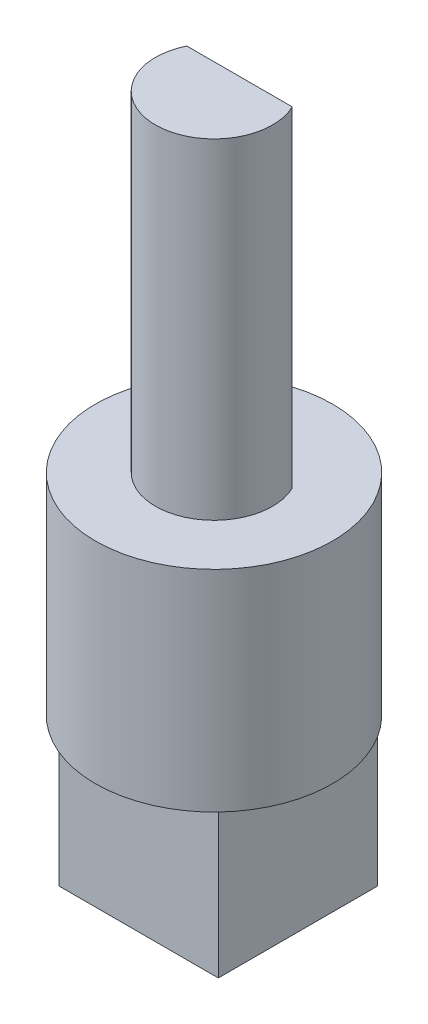
SolidWorks part; units mm, degrees
ref_plane "Front Plane" through (0, 0, 0) normal (0, 0, 1) x (1, 0, 0)
ref_plane "Top Plane" through (0, 0, 0) normal (0, 1, 0) x (1, 0, 0)
ref_plane "Right Plane" through (0, 0, 0) normal (1, 0, 0) x (0, 0, -1)
sketch "Sketch1" plane through (0, 0, 0) normal (0, 1, 0) x (1, 0, 0)
  line L7 (2.65, -2.5069) -> (-2.65, -2.5069)
  line L8 (2.65, -2.5069) -> (2.65, 2.7931)
  line L9 (2.65, 2.7931) -> (-2.65, 2.7931)
  line L10 (-2.65, -2.5069) -> (-2.65, 2.7931)
  line L11 (2.65, -2.5069) -> (-2.65, 2.7931) construction
  line L12 (2.65, 2.7931) -> (-2.65, -2.5069) construction
  point P0 (0, 0)
  dimension "D1" = 5.3
  dimension "D4" = 90
extrude "Boss-Extrude1" add sketch "Sketch1" along normal blind 5
sketch "Sketch2" plane through (0, 5, 0) normal (0, 1, 0) x (1, 0, 0)
  circle A1 centre (0, 0) radius 3.95
  dimension "D1" = 7.9
extrude "Boss-Extrude2" add sketch "Sketch2" along normal blind 7
sketch "Sketch3" plane through (0, 12, 0) normal (0, 1, 0) x (1, 0, 0)
  circle A0 centre (0, 0) radius 1.95
  dimension "D1" = 3.9
extrude "Boss-Extrude3" add sketch "Sketch3" along normal blind 11
sketch "Sketch4" plane through (0, 23, 0) normal (0, 1, 0) x (1, 0, 0)
  line L0 (0, -1.95) -> (0, 0.85) construction
  line L1 (0, 0.85) -> (1.755, 0.85) construction
  line L2 (0, 0.85) -> (-1.755, 0.85) construction
  line L3 (-1.755, 0.85) -> (1.755, 0.85)
  circle A0 centre (0, 0) radius 1.95 construction
  circle A1 centre (0, 0) radius 1.95 construction
  arc A2 (-1.755, 0.85) -> (1.755, 0.85) centre (0, 0) cw
  dimension "D1" = 2.8
extrude "Cut-Extrude1" cut sketch "Sketch4" against normal blind 11
